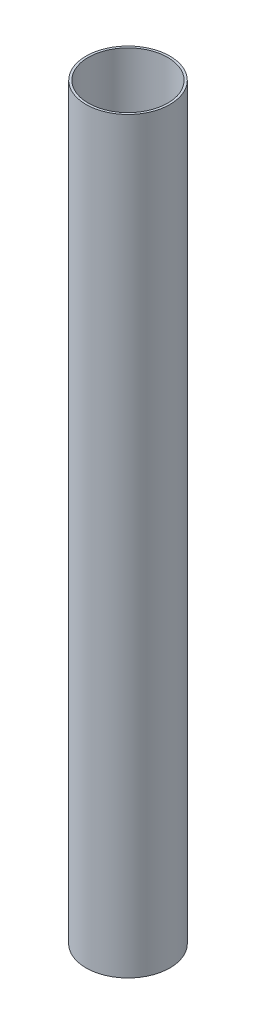
SolidWorks part; units mm, degrees
ref_plane "Front Plane" through (0, 0, 0) normal (0, 0, 1) x (1, 0, 0)
ref_plane "Top Plane" through (0, 0, 0) normal (0, 1, 0) x (1, 0, 0)
ref_plane "Right Plane" through (0, 0, 0) normal (1, 0, 0) x (0, 0, -1)
sketch "Sketch1" plane through (0, 0, 0) normal (0, 0, 1) x (1, 0, 0)
  line L0 (26.9748, 0) -> (28.4988, 0)
  line L1 (28.4988, 0) -> (28.4988, 508)
  line L2 (28.4988, 508) -> (26.9748, 508)
  line L7 (26.9748, 0) -> (26.9748, 508)
  dimension "D1" = 26.9748
  dimension "D2" = 1.524
  dimension "D3" = 508
ref_axis "Central Axis" through (0, 123.6201, 0) along (0, -1, 0)
revolve "Revolve1" add sketch "Sketch1" angle 360 about axis through (0, 123.6201, 0) along (0, -1, 0)
